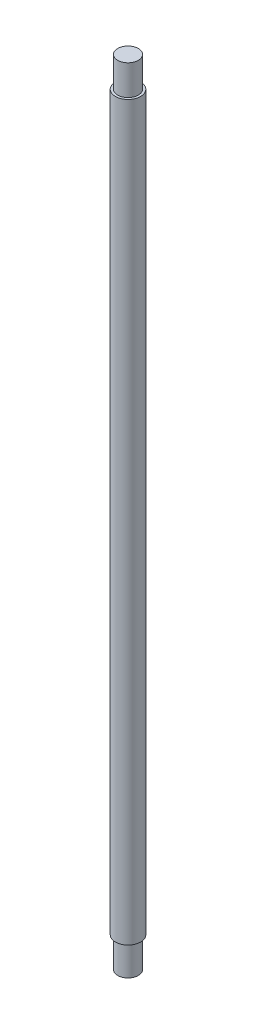
SolidWorks part; units mm, degrees
material "1060-H18"
ref_plane "Front Plane" through (0, 0, 0) normal (0, 0, 1) x (1, 0, 0)
ref_plane "Top Plane" through (0, 0, 0) normal (0, 1, 0) x (1, 0, 0)
ref_plane "Right Plane" through (0, 0, 0) normal (1, 0, 0) x (0, 0, -1)
sketch "Sketch1" plane through (0, 0, 0) normal (0, 1, 0) x (1, 0, 0)
  circle A0 centre (0, 0) radius 82.5
  dimension "D1" = 165
extrude "Boss-Extrude1" add sketch "Sketch1" along normal blind 5195
sketch "Sketch2" plane through (0, 0, 0) normal (0, -1, 0) x (1, 0, 0)
  circle A0 centre (0, 0) radius 82.5
  circle A1 centre (0, 0) radius 67.5
  dimension "D1" = 135
extrude "Cut-Extrude1" cut sketch "Sketch2" against normal blind 197.5
sketch "Sketch3" plane through (0, 5195, 0) normal (0, 1, 0) x (1, 0, 0)
  circle A0 centre (0, 0) radius 82.5
  circle A1 centre (0, 0) radius 67.5
  dimension "D1" = 135
extrude "Cut-Extrude2" cut sketch "Sketch3" against normal blind 197.5
